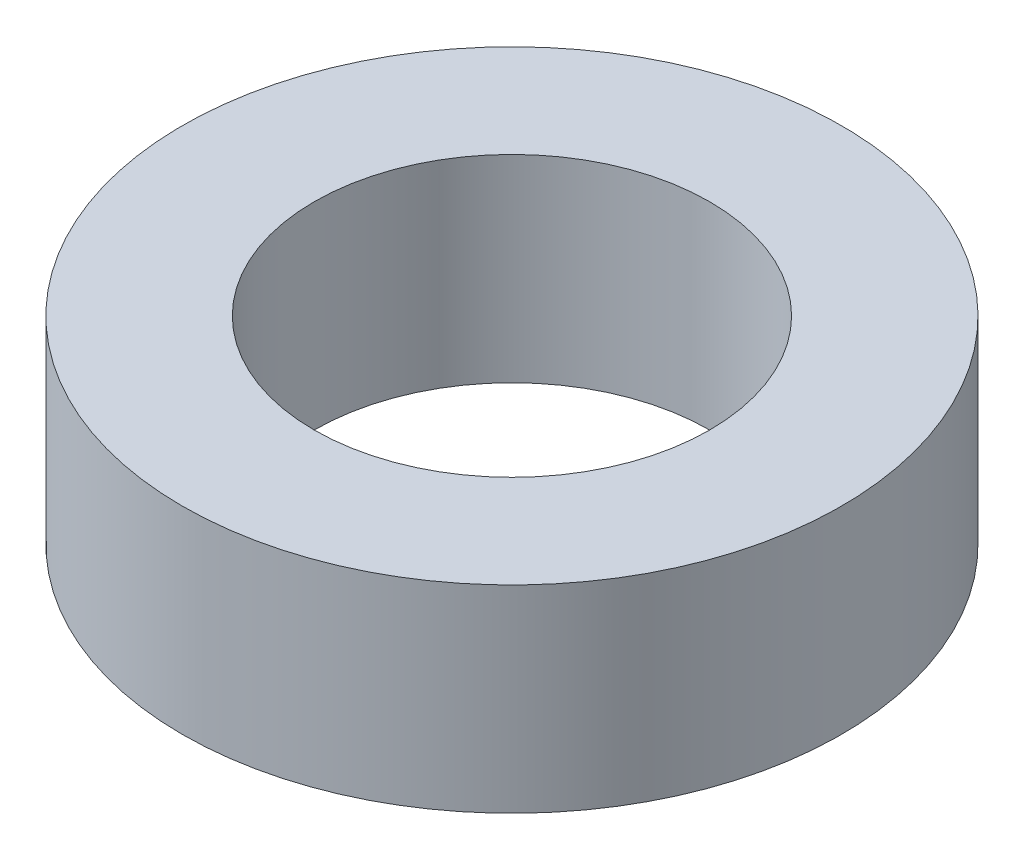
SolidWorks part; units mm, degrees
ref_plane "Front" through (0, 0, 0) normal (0, 0, 1) x (1, 0, 0)
ref_plane "Top" through (0, 0, 0) normal (0, 1, 0) x (1, 0, 0)
ref_plane "Right" through (0, 0, 0) normal (1, 0, 0) x (0, 0, -1)
sketch "Sketch1" plane through (0, 0, 0) normal (0, 1, 0) x (1, 0, 0)
  circle A0 centre (0, 0) radius 5
  circle A1 centre (0, 0) radius 3
  dimension "D1" = 10
  dimension "D2" = 6
extrude "Boss-Extrude1" add sketch "Sketch1" along normal blind 3
